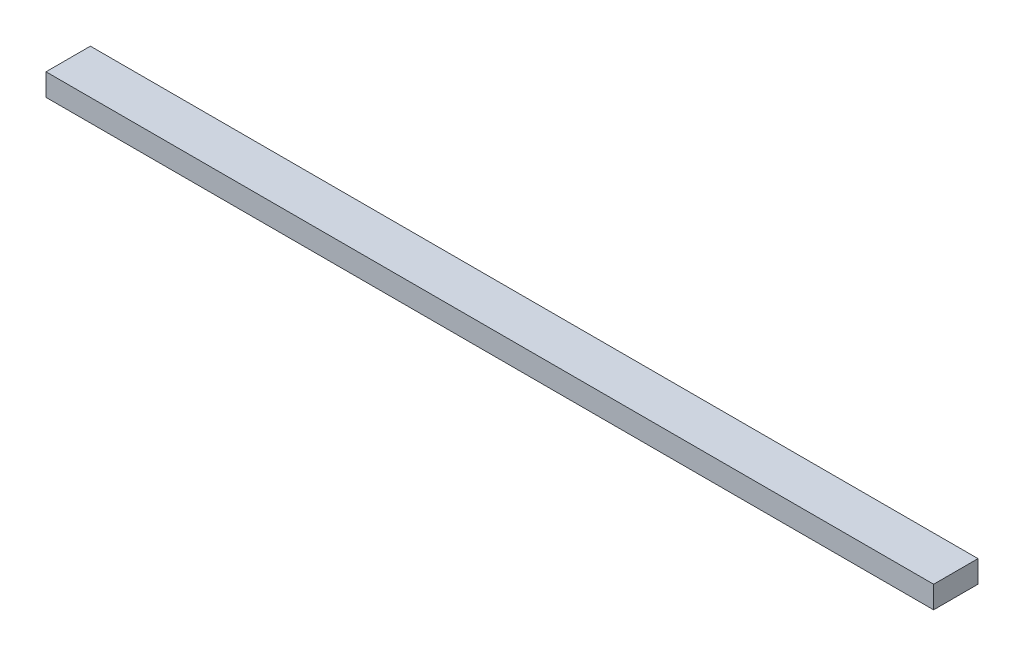
SolidWorks part; units mm, degrees
ref_plane "Front Plane" through (0, 0, 0) normal (0, 0, 1) x (1, 0, 0)
ref_plane "Top Plane" through (0, 0, 0) normal (0, 1, 0) x (1, 0, 0)
ref_plane "Right Plane" through (0, 0, 0) normal (1, 0, 0) x (0, 0, -1)
sketch "Sketch1" plane through (0, 0, 0) normal (0, 1, 0) x (1, 0, 0)
  line L0 (-200, 10) -> (200, -10) construction
  line L1 (-200, 10) -> (200, 10)
  line L2 (-200, 10) -> (-200, -10)
  line L3 (-200, -10) -> (200, -10)
  line L4 (200, 10) -> (200, -10)
  dimension "D1" = 400
  dimension "D2" = 20
extrude "Boss-Extrude1" add sketch "Sketch1" along normal blind 10
